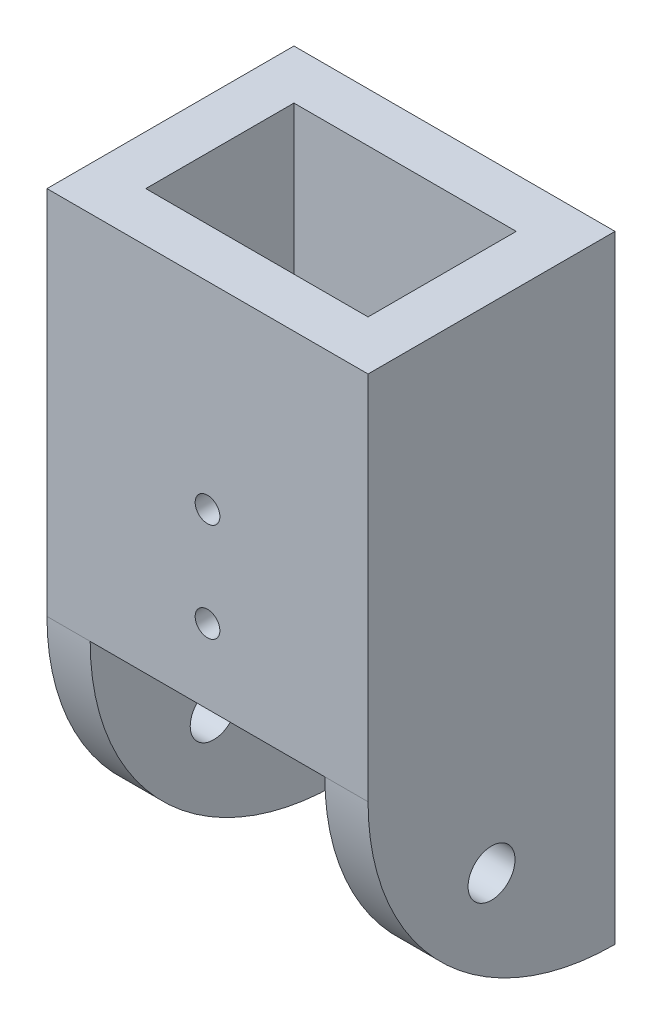
SolidWorks part; units mm, degrees
ref_plane "Front Plane" through (0, 0, 0) normal (0, 0, 1) x (1, 0, 0)
ref_plane "Top Plane" through (0, 0, 0) normal (0, 1, 0) x (1, 0, 0)
ref_plane "Right Plane" through (0, 0, 0) normal (1, 0, 0) x (0, 0, -1)
sketch "Sketch1" plane through (0, 0, 0) normal (0, 1, 0) x (1, 0, 0)
  line L1 (-6.5, -5) -> (6.5, -5)
  line L2 (-6.5, -5) -> (-6.5, 5)
  line L3 (-6.5, 5) -> (6.5, 5)
  line L4 (6.5, -5) -> (6.5, 5)
  line L5 (-6.5, -5) -> (6.5, 5) construction
  line L6 (-6.5, 5) -> (6.5, -5) construction
  line L7 (-4.5, -3) -> (4.5, -3)
  line L8 (-4.5, -3) -> (-4.5, 3)
  line L9 (-4.5, 3) -> (4.5, 3)
  line L10 (4.5, -3) -> (4.5, 3)
  line L11 (-4.5, -3) -> (4.5, 3) construction
  line L12 (-4.5, 3) -> (4.5, -3) construction
  point P0 (0, 0)
  point P6 (0, 0)
  dimension "D1" = 10
  dimension "D2" = 13
  dimension "D3" = 2
  dimension "D4" = 2
extrude "Boss-Extrude1" add sketch "Sketch1" along normal blind 15
sketch "Sketch2" plane through (6.5, 0, 0) normal (1, 0, 0) x (0, 0, -1)
  line L0 (5, 0) -> (5, -10)
  line L2 (-5, 0) -> (5, 0)
  arc A0 (-5, 0) -> (5, -10) centre (5, 0) ccw
  line M2 (-5, 0) -> (5, 0)
  dimension "D1" = 10
extrude "Boss-Extrude2" add sketch "Sketch2" against normal blind 2 contours A0 L0 M2
mirror "Mirror1" about plane through (0, 0, 0) normal (1, 0, 0) of "Boss-Extrude2"
sketch "Sketch3" plane through (6.5, 0, 0) normal (1, 0, 0) x (0, 0, -1)
  line L0 (5.5, 0) -> (-5.5, 0) construction
  line L1 (5, 15) -> (5, -10) construction
  circle A0 centre (0, -5) radius 0.95
  dimension "D1" = 1.9
  dimension "D2" = 5
  dimension "D3" = 5
extrude "Cut-Extrude1" cut sketch "Sketch3" against normal through all
sketch "Sketch4" plane through (0, 0, 5) normal (0, 0, 1) x (1, 0, 0)
  line L0 (0, -5.5) -> (0, 5.5) construction
  line L1 (5.5, 0) -> (-5.5, 0) construction
  circle A0 centre (0, 3) radius 0.5
  circle A1 centre (0, 7) radius 0.5
  dimension "D1" = 1
  dimension "D2" = 1
  dimension "D3" = 3
  dimension "D4" = 4
extrude "Cut-Extrude2" cut sketch "Sketch4" against normal through all
sketch "Sketch5" plane through (0, 0, 0) normal (0, 0, 1) x (1, 0, 0)
  line L0 (5.5, 0) -> (-5.5, 0) construction
  line L1 (-4.5, -10) -> (-4.75, -10)
  line L2 (-4.5, -10) -> (-4.5, 0)
  line L3 (-4.5, 0) -> (-4.75, 0)
  line L4 (-4.75, -10) -> (-4.75, 0)
  line L6 (4.5, -10) -> (4.75, -10)
  line L7 (4.5, -10) -> (4.5, 0)
  line L8 (4.5, 0) -> (4.75, 0)
  line L9 (4.75, -10) -> (4.75, 0)
  dimension "D1" = 0.25
  dimension "D2" = 0.25
extrude "Cut-Extrude3" cut sketch "Sketch5" against normal through all both and the other way through all
